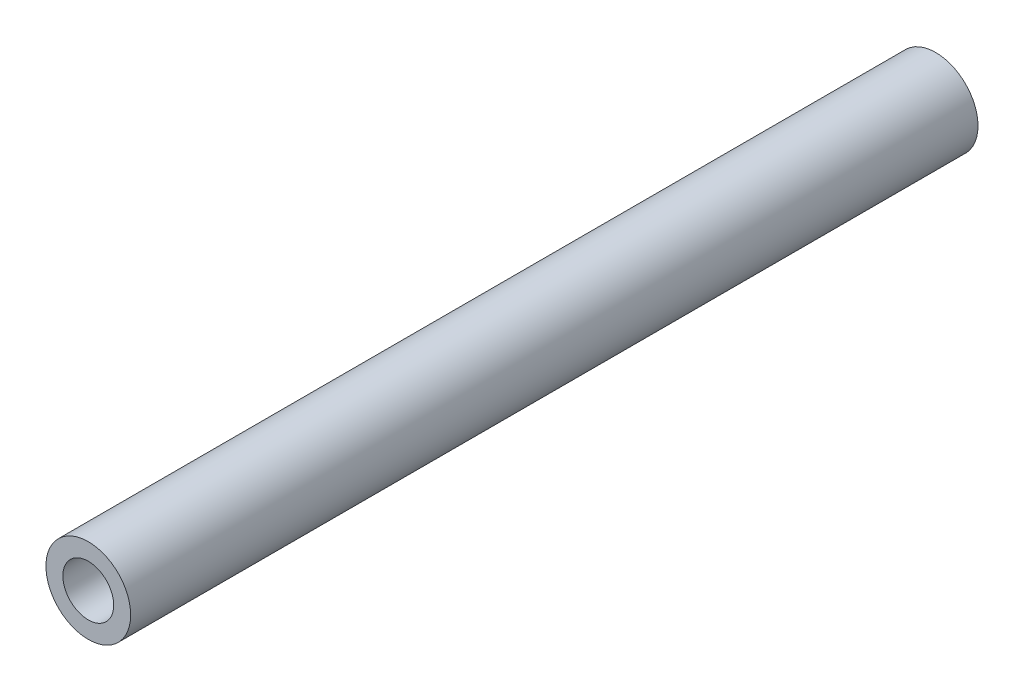
SolidWorks part; units mm, degrees
ref_plane "Front Plane" through (0, 0, 0) normal (0, 0, 1) x (1, 0, 0)
ref_plane "Top Plane" through (0, 0, 0) normal (0, 1, 0) x (1, 0, 0)
ref_plane "Right Plane" through (0, 0, 0) normal (1, 0, 0) x (0, 0, -1)
sketch "Sketch1" plane through (0, 0, 0) normal (0, 0, 1) x (1, 0, 0)
  circle A0 centre (0, 0) radius 150
  circle A1 centre (0, 0) radius 250
  dimension "D1" = 300
  dimension "D2" = 500
extrude "Boss-Extrude1" add sketch "Sketch1" along normal blind 5000
